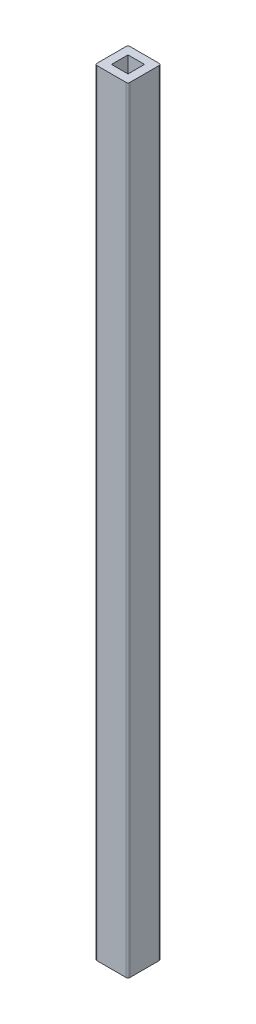
SolidWorks part; units mm, degrees
material "1060 Alloy"
ref_plane "Front Plane" through (0, 0, 0) normal (0, 0, 1) x (1, 0, 0)
ref_plane "Top Plane" through (0, 0, 0) normal (0, 1, 0) x (1, 0, 0)
ref_plane "Right Plane" through (0, 0, 0) normal (1, 0, 0) x (0, 0, -1)
sketch "Sketch1" plane through (0, 0, 0) normal (0, 1, 0) x (1, 0, 0)
  line L0 (-6.35, 6.35) -> (6.35, 6.35)
  line L1 (-12.7, -12.7) -> (12.7, -12.7)
  line L2 (-12.7, -12.7) -> (-12.7, 12.7)
  line L3 (-12.7, 12.7) -> (12.7, 12.7)
  line L4 (12.7, -12.7) -> (12.7, 12.7)
  line L5 (-12.7, -12.7) -> (12.7, 12.7) construction
  line L6 (-12.7, 12.7) -> (12.7, -12.7) construction
  line L7 (6.35, -6.35) -> (6.35, 6.35)
  line L8 (-6.35, -6.35) -> (6.35, -6.35)
  line L9 (-6.35, -6.35) -> (-6.35, 6.35)
  point P0 (0, 0)
  dimension "D1" = 25.4
  dimension "D2" = 6.35
extrude "Boss-Extrude1" add sketch "Sketch1" along normal mid plane 596
fillet "Fillet1" radius 1.5 4 edges at (-12.7, 0, -12.7) (12.7, 0, -12.7) (-12.7, 0, 12.7) (12.7, 0, 12.7)
